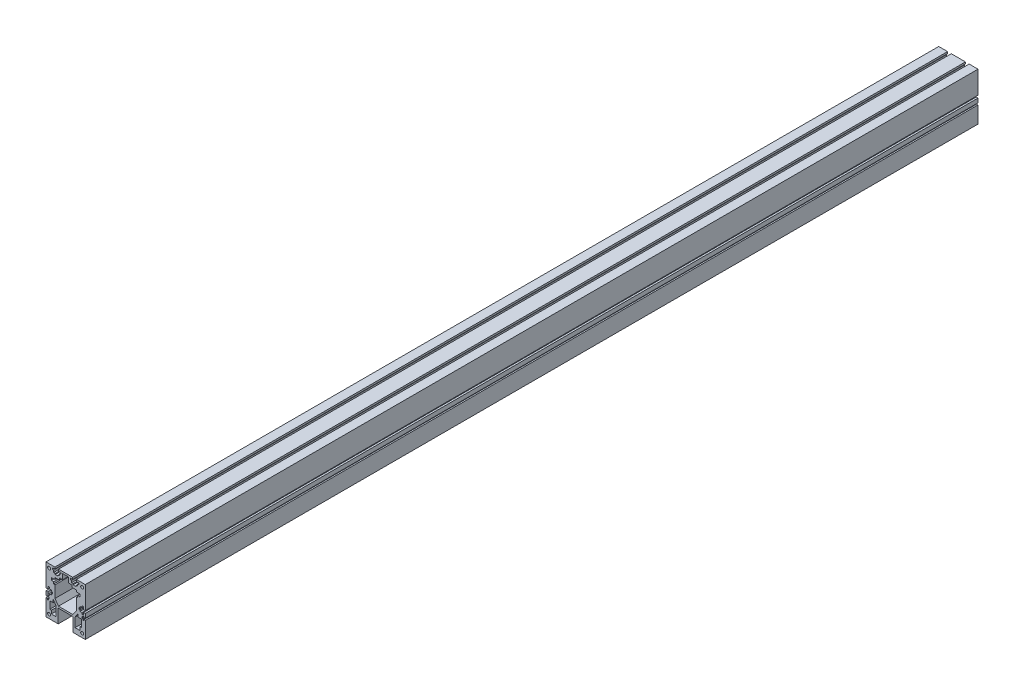
SolidWorks part; units mm, degrees
ref_plane "前视基准面" through (0, 0, 0) normal (0, 0, 1) x (1, 0, 0)
ref_plane "上视基准面" through (0, 0, 0) normal (0, 1, 0) x (1, 0, 0)
ref_plane "右视基准面" through (0, 0, 0) normal (1, 0, 0) x (0, 0, -1)
sketch "草图2" plane through (0, 0, 0) normal (0, 0, 1) x (1, 0, 0)
  line L0 (-18.1, 40) -> (-18.1, 37)
  line L1 (-33, 40) -> (-18.1, 40)
  line L2 (-33, 40) -> (-33, 2.0496)
  line L3 (-33, -40) -> (33, -40)
  line L4 (33, 40) -> (33, 2.0496)
  line L5 (-33, 40) -> (33, -40) construction
  line L6 (-33, -40) -> (33, 40) construction
  line L7 (-27.8, 33.5) -> (27.8, 33.5) construction
  line L8 (-27.8, 33.5) -> (-27.8, -33.5) construction
  line L9 (-27.8, -33.5) -> (27.8, -33.5) construction
  line L10 (27.8, 33.5) -> (27.8, -33.5) construction
  line L11 (-27.8, 33.5) -> (27.8, -33.5) construction
  line L12 (-27.8, -33.5) -> (27.8, 33.5) construction
  line L13 (-18.1, 37) -> (-22.1, 37)
  line L14 (-22.1, 37) -> (-22.1, 34.5)
  line L15 (-22.1, 34.5) -> (-20.1, 34.5)
  line L16 (-20.1, 34.5) -> (-20.1, 31)
  line L17 (-20.1, 31) -> (-17.5, 31)
  line L18 (-17.5, 31) -> (-17.5, 29.4)
  line L19 (-17.5, 29.4) -> (-12.5, 29.4)
  line L20 (-15, 29.4) -> (-15, 48.3161) construction
  line L21 (-12.5, 31) -> (-12.5, 29.4)
  line L22 (-9.9, 31) -> (-12.5, 31)
  line L23 (-9.9, 34.5) -> (-9.9, 31)
  line L24 (-7.9, 34.5) -> (-9.9, 34.5)
  line L25 (-7.9, 37) -> (-7.9, 34.5)
  line L26 (-11.9, 37) -> (-7.9, 37)
  line L27 (-11.9, 40) -> (-11.9, 37)
  line L28 (-11.9, 40) -> (11.9, 40)
  line L29 (0, 0) -> (0, 48.3161) construction
  line L30 (11.9, 40) -> (11.9, 37)
  line L31 (11.9, 37) -> (7.9, 37)
  line L32 (7.9, 37) -> (7.9, 34.5)
  line L33 (7.9, 34.5) -> (9.9, 34.5)
  line L34 (9.9, 34.5) -> (9.9, 31)
  line L35 (9.9, 31) -> (12.5, 31)
  line L36 (12.5, 31) -> (12.5, 29.4)
  line L37 (17.5, 29.4) -> (12.5, 29.4)
  line L38 (17.5, 31) -> (17.5, 29.4)
  line L39 (20.1, 31) -> (17.5, 31)
  line L40 (20.1, 34.5) -> (20.1, 31)
  line L41 (22.1, 34.5) -> (20.1, 34.5)
  line L42 (22.1, 37) -> (22.1, 34.5)
  line L43 (18.1, 37) -> (22.1, 37)
  line L44 (18.1, 40) -> (18.1, 37)
  line L45 (18.1, 40) -> (33, 40)
  line L46 (-24.0002, 21.7881) -> (-17.9322, 21.7881)
  line L47 (-17.9322, 21.7881) -> (-17.9322, 24.7125)
  line L48 (-17.9322, 24.7125) -> (-10.6389, 24.7125)
  line L49 (-10.6389, 24.7125) -> (-10.6389, 28.1692)
  line L50 (-10.6389, 28.1692) -> (-4.9, 28.1692)
  line L51 (-4.9, 28.1692) -> (-4.9, 37)
  line L52 (-4.9, 37) -> (4.9, 37)
  line L53 (-24.0002, 21.7881) -> (-24.0002, 17.5528)
  line L54 (-24.0002, 17.5528) -> (-20.1431, 17.5528)
  line L55 (-20.1431, 17.5528) -> (-20.1431, 14.1747)
  line L56 (-20.1431, 14.1747) -> (-17.9322, 14.1747)
  line L57 (-17.9322, 14.1747) -> (-17.9322, -5.7521)
  line L58 (-17.9322, -5.7521) -> (-12.0458, -14)
  line L59 (-12.0458, -14) -> (0, -14)
  line L60 (0, 0) -> (0, -54.8405) construction
  line L61 (4.9, 28.1692) -> (4.9, 37)
  line L62 (10.6389, 24.7125) -> (10.6389, 28.1692)
  line L63 (10.6389, 28.1692) -> (4.9, 28.1692)
  line L64 (17.9322, 24.7125) -> (10.6389, 24.7125)
  line L65 (17.9322, 21.7881) -> (17.9322, 24.7125)
  line L66 (24.0002, 21.7881) -> (17.9322, 21.7881)
  line L67 (24.0002, 21.7881) -> (24.0002, 17.5528)
  line L68 (27.8, -33.5) -> (-27.8, 33.5) construction
  line L69 (27.8, 33.5) -> (-27.8, -33.5) construction
  line L70 (12.0458, -14) -> (0, -14)
  line L71 (17.9322, -5.7521) -> (12.0458, -14)
  line L72 (17.9322, 14.1747) -> (17.9322, -5.7521)
  line L73 (20.1431, 14.1747) -> (17.9322, 14.1747)
  line L74 (20.1431, 17.5528) -> (20.1431, 14.1747)
  line L75 (24.0002, 17.5528) -> (20.1431, 17.5528)
  line L76 (-12.5, -40) -> (-12.5, -17)
  line L77 (-12.5, -17) -> (12.5, -17)
  line L78 (12.5, -17) -> (12.5, -40)
  line L79 (-33, -2.0496) -> (-30, -2.0496)
  line L80 (-30, -2.0496) -> (-30, -6.3482)
  line L81 (-27.8, -2.7555) -> (-26.6442, -2.7555)
  line L82 (-30, -6.3482) -> (-27.5, -6.3482)
  line L83 (-27.5, -6.3482) -> (-27.5, -3.5932)
  line L84 (-27.5, -3.5932) -> (-24, -3.5932)
  line L85 (-24, -3.5932) -> (-24, -1.3766)
  line L86 (-22.4, -1.3766) -> (-22.4, 1.3766)
  line L87 (-24, 1.3766) -> (-22.4, 1.3766)
  line L88 (-24, 3.5932) -> (-24, 1.3766)
  line L89 (-27.5, 3.5932) -> (-24, 3.5932)
  line L90 (-27.5, 6.3482) -> (-27.5, 3.5932)
  line L91 (-30, 6.3482) -> (-27.5, 6.3482)
  line L92 (-30, 2.0496) -> (-30, 6.3482)
  line L93 (-33, 2.0496) -> (-30, 2.0496)
  line L94 (24, -1.3766) -> (22.4, -1.3766)
  line L95 (33, 2.0496) -> (30, 2.0496)
  line L96 (30, 2.0496) -> (30, 6.3482)
  line L97 (30, 6.3482) -> (27.5, 6.3482)
  line L98 (27.5, 6.3482) -> (27.5, 3.5932)
  line L99 (27.5, 3.5932) -> (24, 3.5932)
  line L100 (24, 3.5932) -> (24, 1.3766)
  line L101 (24, 1.3766) -> (22.4, 1.3766)
  line L102 (22.4, -1.3766) -> (22.4, 1.3766)
  line L103 (24, -3.5932) -> (24, -1.3766)
  line L104 (27.5, -3.5932) -> (24, -3.5932)
  line L105 (27.5, -6.3482) -> (27.5, -3.5932)
  line L106 (30, -6.3482) -> (27.5, -6.3482)
  line L107 (27.8, -2.7555) -> (26.6442, -2.7555)
  line L108 (30, -2.0496) -> (30, -6.3482)
  line L109 (-20.9431, -8.11) -> (-15.8, -15.8603)
  line L110 (-15.8, -15.8603) -> (-15.8, -31.3609)
  line L111 (-15.8, -31.3609) -> (-24, -31.3609)
  line L112 (-24, -31.3609) -> (-24, -25.867)
  line L113 (-24, -25.867) -> (-26.6442, -25.867)
  line L114 (-26.6442, -25.867) -> (-26.6442, -13.4541)
  line L115 (-26.6442, -13.4541) -> (-20.9431, -13.4541)
  line L116 (-20.9431, -13.4541) -> (-20.9431, -8.11)
  line L117 (-33, -9.0684) -> (-30.7298, -9.0684)
  line L118 (-30.7298, -9.0684) -> (-30.7298, -7.473)
  line L119 (-30.7298, -7.473) -> (-29.1441, -7.473)
  line L120 (-29.1441, -7.473) -> (-29.1441, -9.0684)
  line L121 (-29.1441, -9.0684) -> (-27.8, -9.0684)
  line L122 (-27.8, -9.0684) -> (-27.8, -10.5684)
  line L123 (-36.4558, -10.5684) -> (-24.4752, -10.5684) construction
  line L124 (-27.8, -12.0684) -> (-27.8, -9.0684)
  line L125 (-29.1441, -12.0684) -> (-27.8, -12.0684)
  line L126 (-29.1441, -13.6637) -> (-29.1441, -12.0684)
  line L127 (-30.7298, -13.6637) -> (-29.1441, -13.6637)
  line L128 (-30.7298, -12.0684) -> (-30.7298, -13.6637)
  line L129 (-33, -12.0684) -> (-30.7298, -12.0684)
  line L130 (-33, -9.0684) -> (-30.7298, -9.0684)
  line L131 (-30.7298, -9.0684) -> (-30.7298, -7.473)
  line L132 (-30.7298, -7.473) -> (-29.1441, -7.473)
  line L133 (-29.1441, -7.473) -> (-29.1441, -9.0684)
  line L134 (-29.1441, -9.0684) -> (-27.8, -9.0684)
  line L135 (-27.8, -12.0684) -> (-27.8, -10.5684)
  line L136 (-29.1441, -12.0684) -> (-27.8, -12.0684)
  line L137 (-29.1441, -13.6637) -> (-29.1441, -12.0684)
  line L138 (-30.7298, -13.6637) -> (-29.1441, -13.6637)
  line L139 (-30.7298, -12.0684) -> (-30.7298, -13.6637)
  line L140 (-33, -12.0684) -> (-30.7298, -12.0684)
  line L141 (29.1441, -12.0684) -> (27.8, -12.0684)
  line L142 (29.1441, -13.6637) -> (29.1441, -12.0684)
  line L143 (24, -31.3609) -> (24, -25.867)
  line L144 (15.8, -31.3609) -> (24, -31.3609)
  line L145 (15.8, -15.8603) -> (15.8, -31.3609)
  line L146 (20.9431, -13.4541) -> (20.9431, -8.11)
  line L147 (26.6442, -13.4541) -> (20.9431, -13.4541)
  line L148 (26.6442, -25.867) -> (26.6442, -13.4541)
  line L149 (24, -25.867) -> (26.6442, -25.867)
  line L150 (20.9431, -8.11) -> (15.8, -15.8603)
  line L151 (33, -12.0684) -> (30.7298, -12.0684)
  line L152 (30.7298, -12.0684) -> (30.7298, -13.6637)
  line L153 (30.7298, -13.6637) -> (29.1441, -13.6637)
  line L154 (29.1441, -9.0684) -> (27.8, -9.0684)
  line L155 (29.1441, -7.473) -> (29.1441, -9.0684)
  line L156 (30.7298, -7.473) -> (29.1441, -7.473)
  line L157 (30.7298, -9.0684) -> (30.7298, -7.473)
  line L158 (33, -9.0684) -> (30.7298, -9.0684)
  line L159 (33, -12.0684) -> (30.7298, -12.0684)
  line L160 (30.7298, -12.0684) -> (30.7298, -13.6637)
  line L161 (30.7298, -13.6637) -> (29.1441, -13.6637)
  line L162 (27.8, -12.0684) -> (27.8, -9.0684)
  line L163 (27.8, -9.0684) -> (27.8, -10.5684)
  line L164 (29.1441, -9.0684) -> (27.8, -9.0684)
  line L165 (29.1441, -7.473) -> (29.1441, -9.0684)
  line L166 (30.7298, -7.473) -> (29.1441, -7.473)
  line L167 (30.7298, -9.0684) -> (30.7298, -7.473)
  line L168 (33, -9.0684) -> (30.7298, -9.0684)
  line L169 (33, -2.0496) -> (30, -2.0496)
  line L170 (33, 1.2445) -> (33, -9.0684)
  line L171 (33, -12.0684) -> (33, -40)
  line L172 (-22.4, 0) -> (-43.3501, 0) construction
  line L173 (-24, -1.3766) -> (-22.4, -1.3766)
  line L174 (-33, -2.0496) -> (-33, -40)
  circle A0 centre (-27.8, 33.5) radius 2.5
  circle A1 centre (27.8, 33.5) radius 2.5
  circle A2 centre (27.8, -33.5) radius 2.5
  circle A3 centre (-27.8, -33.5) radius 2.5
  point P0 (0, 0)
  point P7 (0, 0)
  point P32 (-18.1, 38.5)
  point P69 (0, 37)
  point P85 (0, -17)
  point P137 (-27.8, -9.8184)
  point P138 (-27.8, -11.3184)
  point P145 (-27.8, -9.8184)
  dimension "D5" = 5
  dimension "D6" = 5
  dimension "D7" = 5
  dimension "D8" = 5
  dimension "D1" = 66
  dimension "D2" = 80
  dimension "D3" = 55.6
  dimension "D4" = 67
  dimension "D9" = 14.2
  dimension "D10" = 6.2
  dimension "D11" = 10.2
  dimension "D12" = 18
  dimension "D13" = 3
  dimension "D14" = 2.5
  dimension "D15" = 10.6
  dimension "D16" = 9
  dimension "D17" = 5
  dimension "D18" = 25
  dimension "D19" = 0
  dimension "D20" = 23
  dimension "D21" = 3
  dimension "D22" = 3
  dimension "D23" = 3
  dimension "D28" = 3.3
  dimension "D29" = 3
  dimension "D30" = 3
  dimension "D31" = 0
  dimension "D32" = 3.5
extrude "凸台-拉伸1" add sketch "草图2" along normal blind 1500
ref_plane "基准面1" through (-15, 0, 0) normal (1, 0, 0) x (0, 0, -1)
ref_plane "基准面2" through (0, 0, 750) normal (0, 0, -1) x (-1, 0, 0)
